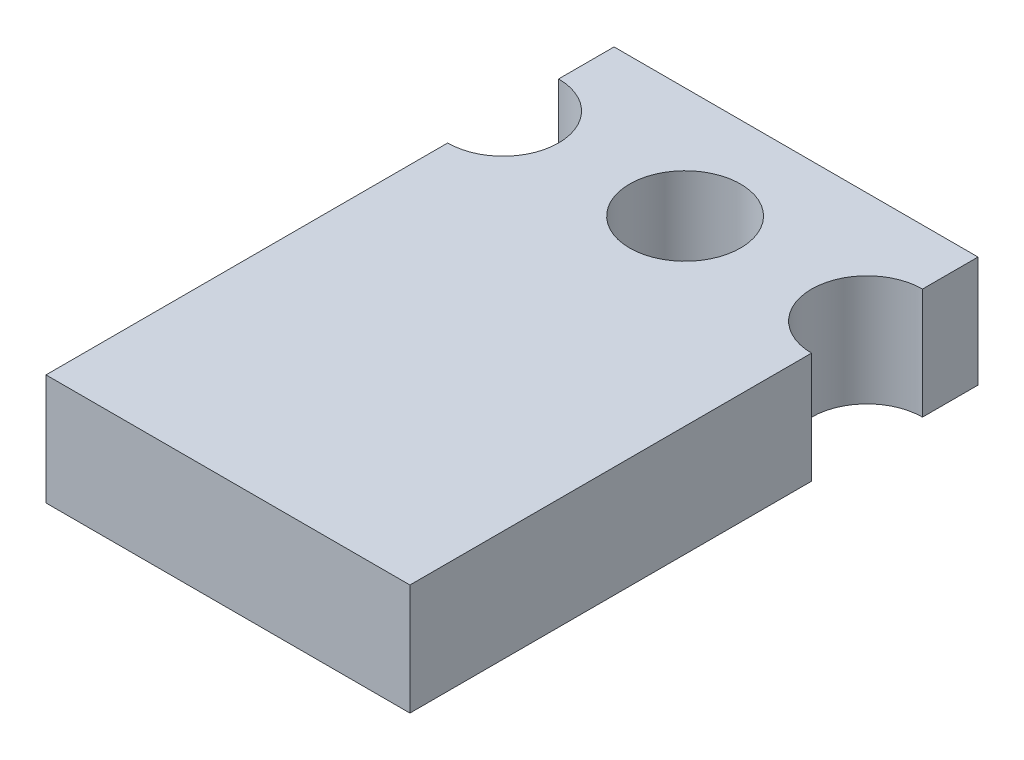
SolidWorks part; units mm, degrees
material "PCB (FR-4) (Recolor-Black)"
ref_plane "Front Plane" through (0, 0, 0) normal (0, 0, 1) x (1, 0, 0)
ref_plane "Top Plane" through (0, 0, 0) normal (0, 1, 0) x (1, 0, 0)
ref_plane "Right Plane" through (0, 0, 0) normal (1, 0, 0) x (0, 0, -1)
sketch "Sketch1" plane through (0, 0, 0) normal (0, 1, 0) x (1, 0, 0)
  line L1 (0, 0) -> (10.414, 0)
  line L2 (0, 0) -> (0, 16.256)
  line L3 (0, 16.256) -> (10.414, 16.256)
  line L4 (10.414, 0) -> (10.414, 16.256)
  dimension "D1" = 10.414
  dimension "D2" = 16.256
extrude "Boss-Extrude1" add sketch "Sketch1" along normal blind 3.175 contours L2 L3 L4 L1
sketch "Sketch2" plane through (0, 3.175, 0) normal (0, 1, 0) x (1, 0, 0)
  line L0 (0, 13.081) -> (10.414, 13.081) construction
  line L1 (0, 0) -> (0, 16.256) construction
  line L2 (10.414, 0) -> (10.414, 16.256) construction
  line L3 (0, 16.256) -> (10.414, 16.256) construction
  circle A0 centre (5.207, 13.081) radius 1.5875
  circle A1 centre (10.414, 13.081) radius 1.5875
  circle A2 centre (0, 13.081) radius 1.5875
  dimension "D2" = 3.175
  dimension "D1" = 3.175
extrude "Cut-Extrude1" cut sketch "Sketch2" against normal blind 3.175
sketch "Sketch3" plane through (0, 0, 0) normal (0, 0, 1) x (1, 0, 0)
  line L0 (0, 0) -> (10.414, 0) construction
  line L1 (8.4201, 1.778) -> (7.0739, 1.778)
  line L2 (8.4201, 1.778) -> (8.4201, 2.413)
  line L3 (8.4201, 2.413) -> (7.0739, 2.413)
  line L4 (7.0739, 1.778) -> (7.0739, 2.413)
  line L5 (3.3401, 1.778) -> (1.9939, 1.778)
  line L6 (3.3401, 1.778) -> (3.3401, 2.413)
  line L7 (3.3401, 2.413) -> (1.9939, 2.413)
  line L8 (1.9939, 1.778) -> (1.9939, 2.413)
  line L9 (2.667, 2.413) -> (2.667, 1.778) construction
  line L10 (7.747, 2.413) -> (7.747, 1.778) construction
  line L11 (5.207, 0) -> (5.207, 3.175) construction
  line L12 (0, 3.175) -> (10.414, 3.175) construction
  line L13 (2.667, 2.0955) -> (7.747, 2.0955) construction
  point P20 (5.207, 2.0955)
  point P21 (5.207, 2.0955)
  dimension "D1" = 1.778
  dimension "D2" = 0.635
  dimension "D3" = 1.3462
  dimension "D4" = 5.08
extrude "Boss-Extrude2" [suppressed] add sketch "Sketch3" along normal blind 12.7
sketch "Sketch4" [suppressed] plane through (0, 2.413, 0) normal (0, 1, 0) x (1, 0, 0)
  line L0 (3.3401, -12.7) -> (3.3401, 0) construction
  line L1 (1.9939, -12.7) -> (2.286, -12.7)
  line L2 (1.9939, -12.7) -> (1.9939, -3.302)
  line L3 (1.9939, -3.302) -> (2.286, -3.302)
  line L4 (2.286, -12.7) -> (2.286, -3.302)
  line L5 (3.3401, -12.7) -> (3.048, -12.7)
  line L6 (3.3401, -12.7) -> (3.3401, -3.302)
  line L7 (3.3401, -3.302) -> (3.048, -3.302)
  line L8 (3.048, -12.7) -> (3.048, -3.302)
  line L9 (3.3401, -12.7) -> (1.9939, -12.7) construction
  line L10 (3.3401, 0) -> (1.9939, 0) construction
  line L11 (7.0739, -12.7) -> (7.366, -12.7)
  line L12 (7.0739, -12.7) -> (7.0739, -3.302)
  line L13 (7.0739, -3.302) -> (7.366, -3.302)
  line L14 (7.366, -12.7) -> (7.366, -3.302)
  line L15 (8.4201, -12.7) -> (8.128, -12.7)
  line L16 (8.4201, -12.7) -> (8.4201, -3.302)
  line L17 (8.4201, -3.302) -> (8.128, -3.302)
  line L18 (8.128, -12.7) -> (8.128, -3.302)
  point P23 (0, 0)
  dimension "D1" = 3.302
  dimension "D2" = 0.762
extrude "Cut-Extrude2" [suppressed] cut sketch "Sketch4" against normal through all
sketch "Sketch5" plane through (0, 0, 0) normal (0, -1, 0) x (1, 0, 0)
  line L0 (5.207, -1.27) -> (5.207, -8.89) construction
  line L1 (9.017, -1.27) -> (1.397, -1.27)
  line L2 (9.017, -1.27) -> (9.017, -8.89)
  line L3 (9.017, -8.89) -> (1.397, -8.89)
  line L4 (1.397, -1.27) -> (1.397, -8.89)
  line L5 (5.207, -1.27) -> (5.207, 0) construction
  line L6 (0, 0) -> (10.414, 0) construction
  dimension "D1" = 7.62
  dimension "D2" = 7.62
  dimension "D3" = 1.27
extrude "Cut-Extrude3" [suppressed] cut sketch "Sketch5" against normal blind 0.635
